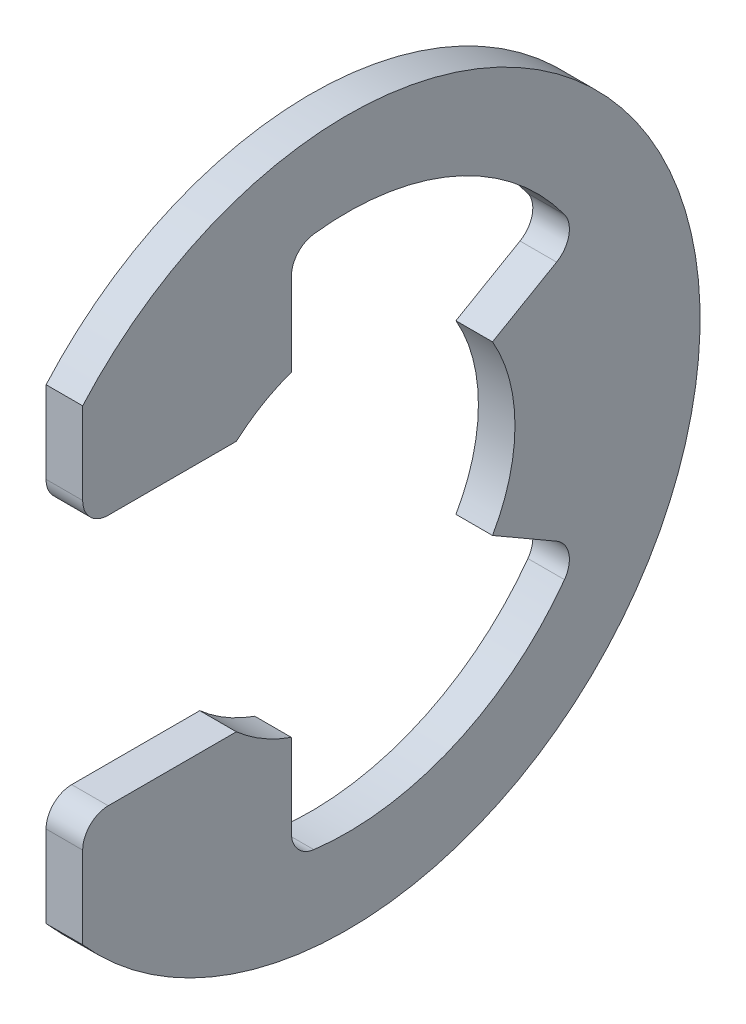
SolidWorks part; units mm, degrees
material "Plain Carbon Steel"
ref_plane "Front" through (0, 0, 0) normal (0, 0, 1) x (1, 0, 0)
ref_plane "Top" through (0, 0, 0) normal (0, 1, 0) x (1, 0, 0)
ref_plane "Right" through (0, 0, 0) normal (1, 0, 0) x (0, 0, -1)
sketch "Sketch1" plane through (0, 0, 0) normal (1, 0, 0) x (0, 0, -1)
  line L0 (-3.2341, 3.6671) -> (-7.7153, 3.6671)
  line L1 (-7.7153, 6.8042) -> (-7.7153, 3.6671)
  line L2 (-7.7153, -6.8042) -> (-7.7153, -3.6671)
  line L3 (-7.7153, -3.6671) -> (-3.2341, -3.6671)
  line L4 (4.2344, -2.4448) -> (6.7836, -3.9165)
  line L5 (4.2344, 2.4448) -> (6.7836, 3.9165)
  line L6 (0, 0) -> (-10.541, 0) construction
  line L7 (4.2344, 2.4448) -> (4.2344, -2.4448) construction
  line L8 (-1.6298, -4.6099) -> (-1.6298, -7.6616)
  line L9 (0, 10.287) -> (0, -10.287) construction
  line L10 (-1.6298, 7.6616) -> (-1.6298, 4.6099)
  circle A1 centre (0, 0) radius 10.541 construction
  circle A2 centre (0, 0) radius 4.8895 construction
  arc A3 (-7.7153, -6.8042) -> (-7.7153, 6.8042) centre (0, 0) ccw
  arc A4 (-3.2341, -3.6671) -> (-1.6298, -4.6099) centre (0, 0) ccw
  arc A5 (-3.2341, 3.6671) -> (-1.6298, 4.6099) centre (0, 0) cw
  arc A6 (4.2344, 2.4448) -> (4.2344, -2.4448) centre (0, 0) cw
  arc A7 (-1.6298, -7.6616) -> (6.7836, -3.9165) centre (0, 0) ccw
  arc A8 (6.7836, 3.9165) -> (-1.6298, 7.6616) centre (0, 0) ccw
  dimension "D1" = 7.833
  dimension "OD" = 20.574
  dimension "L" = 21.082
  dimension "D" = 9.779
  dimension "D5" = 1.6298
  dimension "D2" = 60
  dimension "D3" = 7.3342
  dimension "D4" = 18.0023
extrude "Extrude1" add sketch "Sketch1" along normal mid plane 1.0668
fillet "Fillet1" radius 0.7468 6 edges at (0, -3.9165, -6.7836) (0, 3.9165, -6.7836) (0, -3.6671, 7.7153) (0, -7.6616, 1.6298) (0, 3.6671, 7.7153) (0, 7.6616, 1.6298)
sketch "Sketch3" plane through (0, 0, 0) normal (0, 1, 0) x (1, 0, 0)
  line L0 (0.5842, 6.35) -> (0.5842, 5.0292)
  line L1 (0.5842, 5.0292) -> (-0.5842, 5.0292)
  line L2 (-0.5842, 5.0292) -> (-0.5842, 6.35)
  line L3 (-0.5842, 6.35) -> (-8.1788, 6.35)
  line L4 (3.5052, 0) -> (3.5052, 5.6896)
  line L5 (-8.1788, 6.35) -> (-8.1788, 0)
  line L6 (-8.1788, 0) -> (3.5052, 0)
  line L8 (3.5052, 0) -> (3.5052, 6.35) construction
  line L9 (3.5052, 6.35) -> (0.5842, 6.35) construction
  line L10 (3.5052, 0) -> (17.2631, 0) construction
  line L11 (3.5052, 5.6896) -> (2.8448, 6.35)
  line L12 (2.8448, 6.35) -> (0.5842, 6.35)
  point P2 (0, 5.0292)
  point P5 (0.5842, 5.6896)
  dimension "D1" = 2.921
  dimension "Ds" = 12.7
  dimension "Dg" = 10.0584
  dimension "W" = 1.1684
  dimension "D2" = 11.684
  dimension "D3" = 45
revolve "Revolve2" [suppressed] add sketch "Sketch3" angle 360 about L10
equation "\"D2@Sketch3\" = \"W@Sketch3\"*10"
equation "\"D1@Sketch3\" = \"D2@Sketch3\"/4"
equation "\"D1@Sketch1\" = (\"OD@Sketch1\"+\"D@Sketch1\")/3.875"
equation "\"D3@Sketch1\" = \"D@Sketch1\"*.75"
equation "\"D1@Fillet1\" = \"D1@Extrude1\"*.7"
equation "\"D4@Sketch1\" = \"OD@Sketch1\"*.875"
equation "\"D5@Sketch1\" = \"D@Sketch1\"/6"
